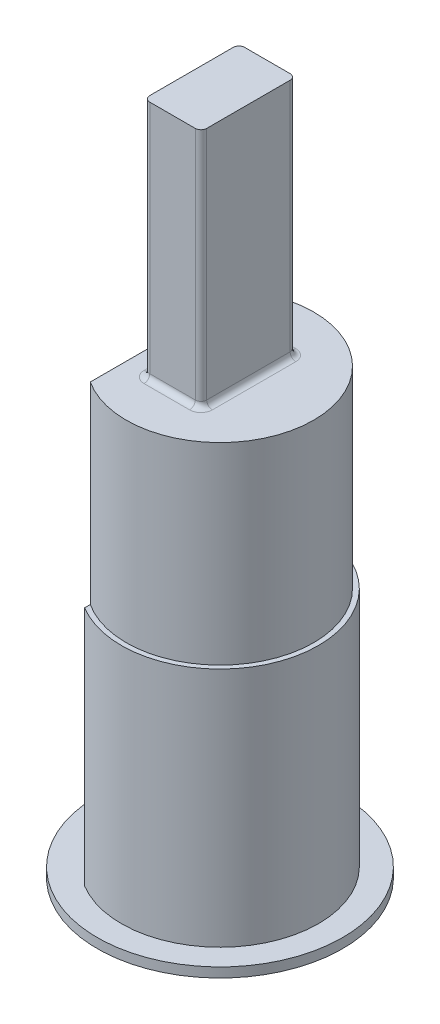
SolidWorks part; units mm, degrees
ref_plane "Front Plane" through (0, 0, 0) normal (0, 0, 1) x (1, 0, 0)
ref_plane "Top Plane" through (0, 0, 0) normal (0, 1, 0) x (1, 0, 0)
ref_plane "Right Plane" through (0, 0, 0) normal (1, 0, 0) x (0, 0, -1)
sketch "Sketch1" plane through (0, 0, 0) normal (0, 1, 0) x (1, 0, 0)
  line L0 (-2.69, 4.445) -> (-2.69, -4.445)
  arc A0 (-2.69, -4.445) -> (-2.69, 4.445) centre (0, 0) ccw
  dimension "D1" = 10.3911
  dimension "D2" = 8.89
extrude "Boss-Extrude1" add sketch "Sketch1" along normal blind 22.86
sketch "Sketch2" plane through (0, 22.86, 0) normal (0, 1, 0) x (1, 0, 0)
  line L1 (-1.2, -2.5) -> (1.2, -2.5)
  line L2 (-1.5, -2.2) -> (-1.5, 2.2)
  line L3 (-1.2, 2.5) -> (1.2, 2.5)
  line L4 (1.5, -2.2) -> (1.5, 2.2)
  line L5 (-1.5, -2.5) -> (1.5, 2.5) construction
  line L6 (-1.5, 2.5) -> (1.5, -2.5) construction
  arc A0 (-1.2, -2.5) -> (-1.5, -2.2) centre (-1.2, -2.2) cw
  arc A1 (1.2, -2.5) -> (1.5, -2.2) centre (1.2, -2.2) ccw
  arc A2 (1.2, 2.5) -> (1.5, 2.2) centre (1.2, 2.2) cw
  arc A3 (-1.5, 2.2) -> (-1.2, 2.5) centre (-1.2, 2.2) cw
  point P0 (0, 0)
  dimension "D3" = 0.3
  dimension "D1" = 5
  dimension "D2" = 3
extrude "Boss-Extrude2" add sketch "Sketch2" along normal blind 12.7
fillet "Fillet1" radius 0.3 8 edges at (1.4121, 22.86, 2.4121) (0, 22.86, 2.5) (-1.4121, 22.86, 2.4121) (-1.5, 22.86, 0) (-1.4121, 22.86, -2.4121) (0, 22.86, -2.5) (1.4121, 22.86, -2.4121) (1.5, 22.86, 0)
sketch "Sketch3" plane through (0, 0, 0) normal (0, -1, 0) x (1, 0, 0)
  circle A0 centre (0, 0) radius 6.4656
  arc A1 (-2.69, -4.445) -> (-2.69, 4.445) centre (0, 0) ccw construction
  dimension "D1" = 1.27
extrude "Boss-Extrude3" add sketch "Sketch3" along normal blind 0.508
sketch "Sketch4" plane through (0, 22.86, 0) normal (0, 1, 0) x (1, 0, 0)
  circle A0 centre (0, 0) radius 4.9416
  arc A1 (-2.69, -4.445) -> (-2.69, 4.445) centre (0, 0) ccw construction
  dimension "D1" = 0.254
extrude "Cut-Extrude1" cut sketch "Sketch4" against normal blind 10.16 flip side to cut
